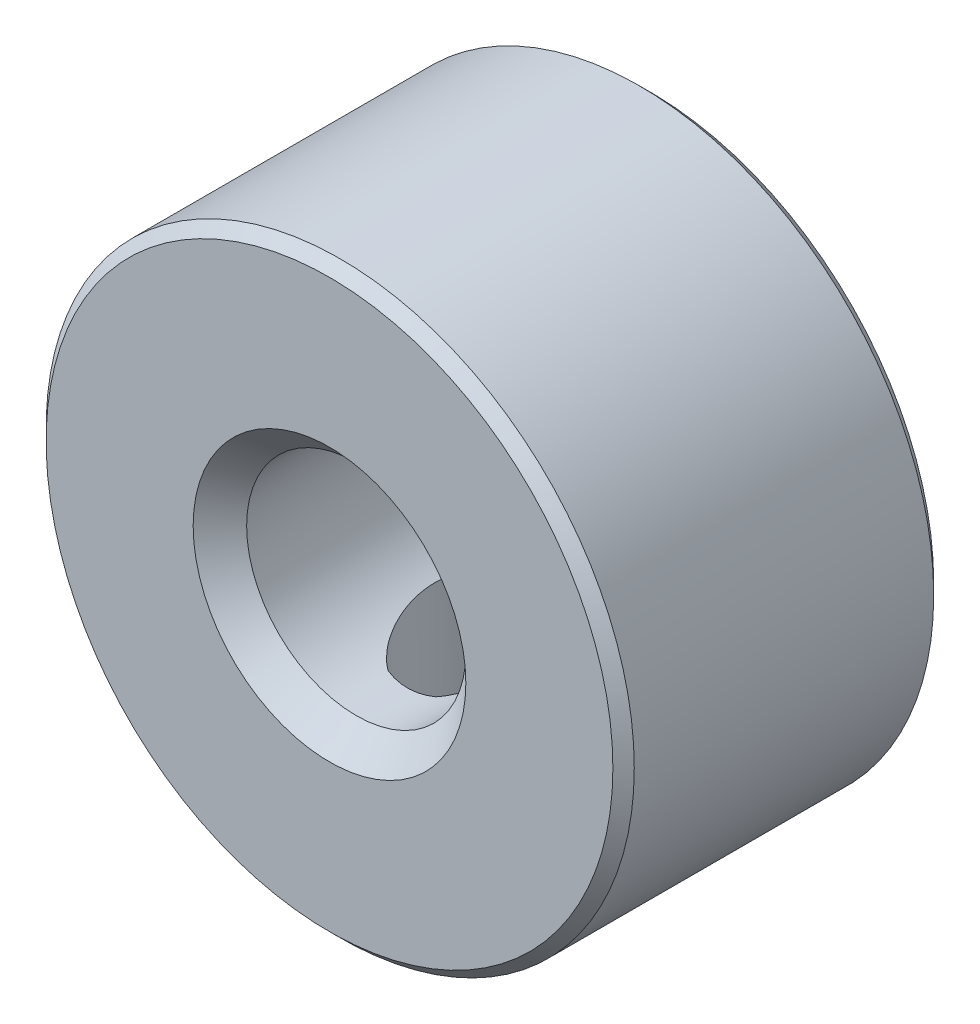
SolidWorks part; units mm, degrees
ref_plane "Front Plane" through (0, 0, 0) normal (0, 0, 1) x (1, 0, 0)
ref_plane "Top Plane" through (0, 0, 0) normal (0, 1, 0) x (1, 0, 0)
ref_plane "Right Plane" through (0, 0, 0) normal (1, 0, 0) x (0, 0, -1)
sketch "Sketch1" plane through (0, 0, 0) normal (0, 0, 1) x (1, 0, 0)
  circle A0 centre (0, 0) radius 5.5
  circle A1 centre (0, 0) radius 2.05
  dimension "D1" = 11
  dimension "D2" = 4.1
extrude "Boss-Extrude1" add sketch "Sketch1" along normal blind 6
chamfer "Chamfer1" distance 0.5 angle 45 2 edges at (2.05, 0, 6) (2.05, 0, 0)
hole_wizard "M4x0.7 Tapped Hole1" positions "3DSketch1" profile "Sketch2" tap size "M4x0.7" standard "ANSI Metric"
sketch3d "3DSketch1"
  point P0 (0.1567, -5.4978, 2.9247)
sketch "Sketch2" plane through (0.1567, -5.4978, 2.9247) normal (0, 0, 1) x (0.9996, 0.0285, 0)
  line L0 (0, 0) -> (0, 4.4914)
  line L1 (0, 4.4914) -> (1.65, 3.5)
  line L2 (1.65, 3.5) -> (1.65, 0)
  line L5 (1.65, 0) -> (0, 0)
  line L10 (0, 4.4914) -> (-1.65, 3.5) construction
  line L11 (0, -6.35) -> (0, 107.95) construction
  dimension "Tap Drill Dia." = 3.3
  dimension "Tap Drill Depth" = 3.5
  dimension "Drill Angle" = 118
cosmetic thread "Hole Thread1" parameters "D1"=3.5, "D2"=4
chamfer "Chamfer2" distance 0.2 angle 45 2 edges at (5.5, 0, 0) (5.5, 0, 6)
